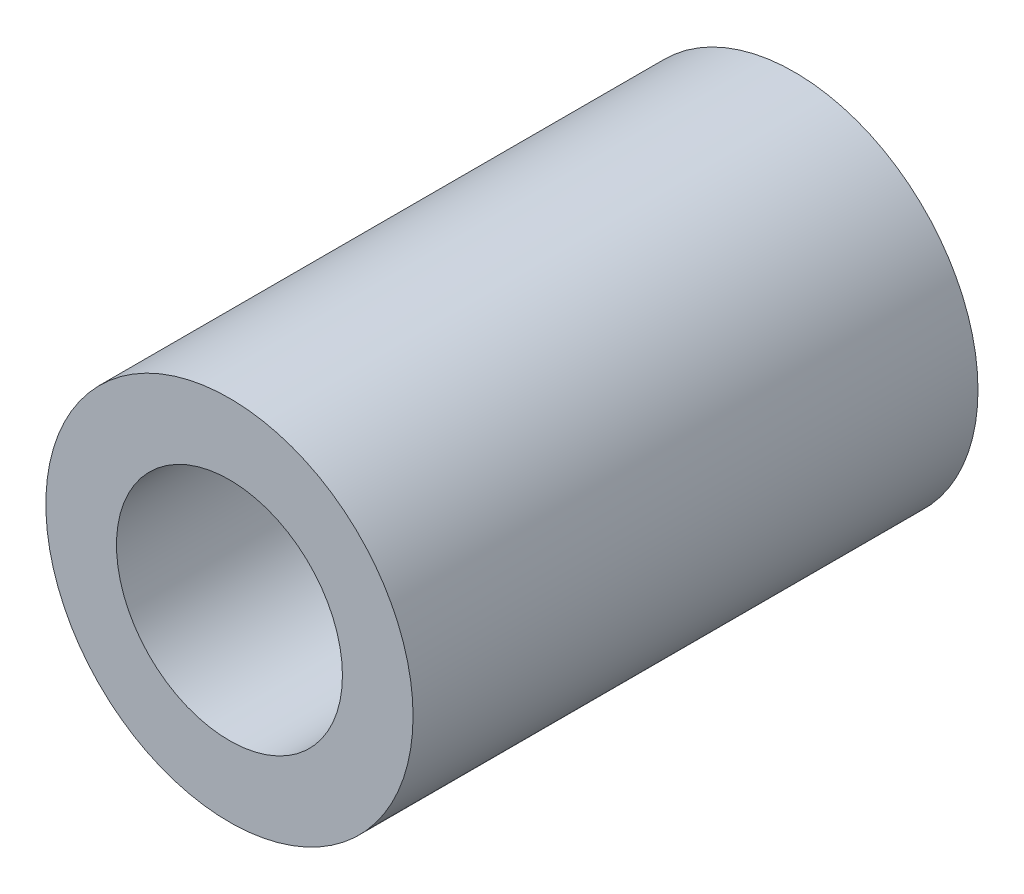
SolidWorks part; units mm, degrees
ref_plane "Plan de face" through (0, 0, 0) normal (0, 0, 1) x (1, 0, 0)
ref_plane "Plan de dessus" through (0, 0, 0) normal (0, 1, 0) x (1, 0, 0)
ref_plane "Plan de droite" through (0, 0, 0) normal (1, 0, 0) x (0, 0, -1)
sketch "Sketch1" plane through (0, 0, 0) normal (0, 0, 1) x (1, 0, 0)
  circle A0 centre (0, 0) radius 2
  circle A1 centre (0, 0) radius 3.25
  dimension "D1" = 4
  dimension "D2" = 6.5
extrude "Boss-Extrude1" add sketch "Sketch1" along normal blind 10
